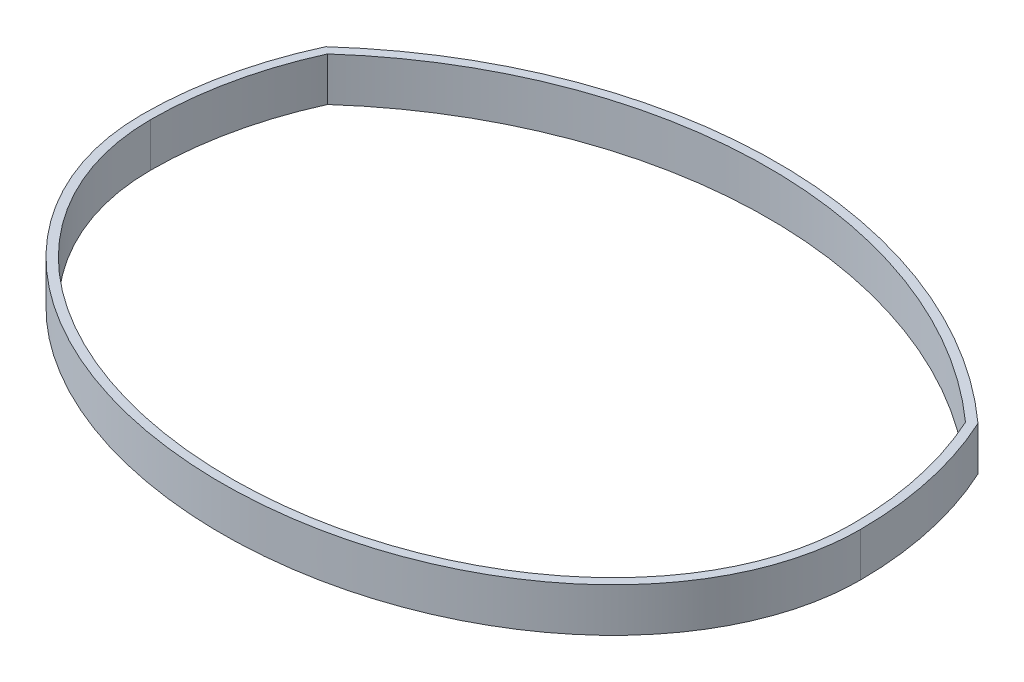
SolidWorks part; units mm, degrees
ref_plane "Front Plane" through (0, 0, 0) normal (0, 0, 1) x (1, 0, 0)
ref_plane "Top Plane" through (0, 0, 0) normal (0, 1, 0) x (1, 0, 0)
ref_plane "Right Plane" through (0, 0, 0) normal (1, 0, 0) x (0, 0, -1)
sketch "Sketch1" plane through (0, 0, 0) normal (0, 1, 0) x (1, 0, 0)
  line L0 (0, 118.5937) -> (0, 77.4941)
  arc A0 (-92.4508, 42.1356) -> (-101.6, 0) centre (0, 0) ccw
  arc A1 (92.4508, 42.1356) -> (-92.4508, 42.1356) centre (0, -61.0492) ccw
  arc A3 (101.6, 0) -> (92.4508, 42.1356) centre (0, 0) ccw
  arc A4 (94.5401, 43.6726) -> (-94.5401, 43.6726) centre (0, -61.0492) ccw
  arc A5 (-94.5401, 43.6726) -> (-104.14, 0) centre (0, 0) ccw
  arc A6 (104.14, 0) -> (94.5401, 43.6726) centre (0, 0) ccw
  ellipse E0 centre (0, 0) end of major axis (-101.6, 0) minor radius 78.4079 (-101.6, 0) -> (101.6, 0) ccw
  spline S0 degree 1 poles (-104.14, 0) (104.14, 0) knots 0 0 1 1 construction
  spline S1 degree 3 poles (-104.14, 0) (-104.14, -5.3532) (-102.774, -16.0383) (-96.7254, -31.4196) (-86.9495, -45.523) (-69.4996, -61.9331) (-40.6644, -76.7914) (0, -83.0262) (40.6644, -76.7914) (69.4996, -61.9331) (86.9495, -45.523) (96.7254, -31.4196) (102.774, -16.0383) (104.14, -5.3532) (104.14, 0) knots 0 0 0 0 0.19635 0.392699 0.589049 0.785398 1.178097 1.570796 1.963495 2.356194 2.552544 2.748894 2.945243 3.141593 3.141593 3.141593 3.141593
  point P10 (0, -78.4079)
  dimension "D2" = 2.54
  dimension "D1" = 203.2
extrude "Boss-Extrude1" add sketch "Sketch1" along normal blind 12.7
